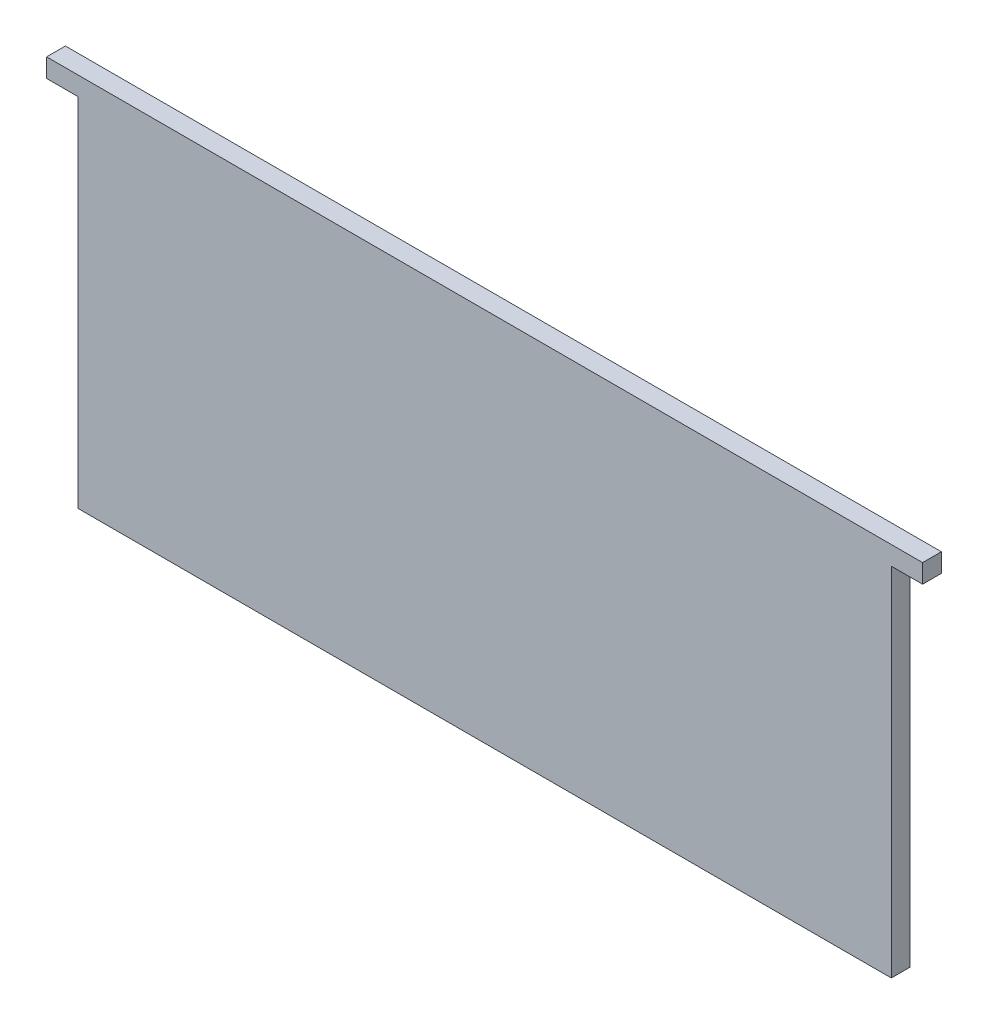
SolidWorks part; units mm, degrees
ref_plane "Front Plane" through (0, 0, 0) normal (0, 0, 1) x (1, 0, 0)
ref_plane "Top Plane" through (0, 0, 0) normal (0, 1, 0) x (1, 0, 0)
ref_plane "Right Plane" through (0, 0, 0) normal (1, 0, 0) x (0, 0, -1)
sketch "Sketch2" plane through (0, 0, 0) normal (0, 0, 1) x (1, 0, 0)
  line L0 (65, 30) -> (70, 30)
  line L1 (65, -30) -> (-65, -30)
  line L2 (65, -30) -> (65, 30)
  line L3 (65, 30) -> (-65, 30)
  line L4 (-65, -30) -> (-65, 30)
  line L5 (65, -30) -> (-65, 30) construction
  line L6 (65, 30) -> (-65, -30) construction
  line L7 (70, 30) -> (70, 27)
  line L8 (70, 27) -> (65, 27)
  line L9 (65, 27) -> (65, 30)
  line L10 (-65, 30) -> (-70, 30)
  line L11 (-70, 30) -> (-70, 27)
  line L12 (-70, 27) -> (-65, 27)
  line L13 (-65, 27) -> (-65, 30)
  point P0 (0, 0)
  dimension "D1" = 130
  dimension "D2" = 60
  dimension "D3" = 3
  dimension "D4" = 3
  dimension "D5" = 5
  dimension "D6" = 5
extrude "Boss-Extrude1" add sketch "Sketch2" along normal blind 3 contours L4 L1 L2 L3 | L8 L7 L0 L2 | L11 L12 L4 L10
